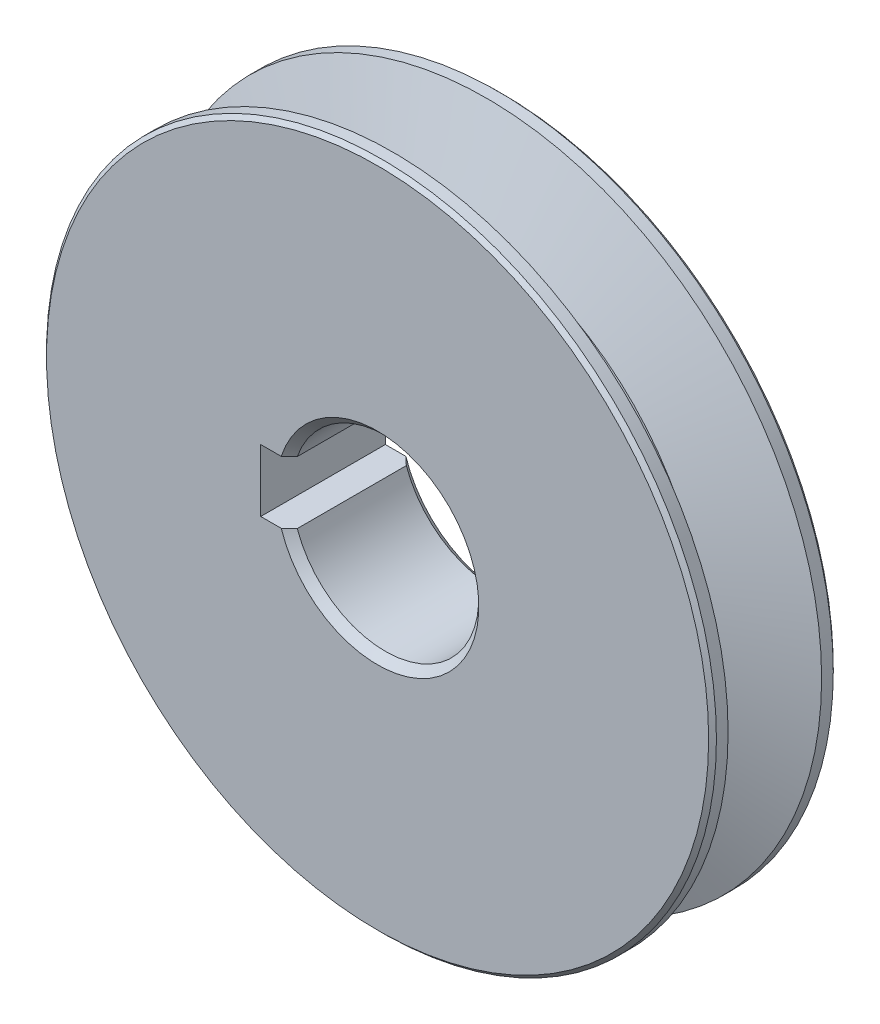
SolidWorks part; units mm, degrees
ref_plane "Front Plane" through (0, 0, 0) normal (0, 0, 1) x (1, 0, 0)
ref_plane "Top Plane" through (0, 0, 0) normal (0, 1, 0) x (1, 0, 0)
ref_plane "Right Plane" through (0, 0, 0) normal (1, 0, 0) x (0, 0, -1)
sketch "Sketch1" plane through (0, 0, 0) normal (0, 1, 0) x (1, 0, 0)
  line L0 (43, 8) -> (0, 8)
  line L1 (0, 8) -> (0, -8)
  line L2 (0, -8) -> (43, -8)
  line L3 (43, -8) -> (43, -6.0037)
  line L4 (43, -6.0037) -> (32, -2)
  line L5 (32, -2) -> (32, 2)
  line L6 (32, 2) -> (43, 6.0037)
  line L7 (43, 6.0037) -> (43, 8)
  line L8 (0, 8) -> (0, -8) construction
revolve "Revolve1" add sketch "Sketch1" angle 360 about L8
sketch "Sketch2" plane through (0, 0, 8) normal (0, 0, 1) x (1, 0, 0)
  line L0 (-15, -4) -> (-11.3137, -4)
  line L1 (-11.3137, 4) -> (-15, 4)
  line L2 (-15, 4) -> (-15, -4)
  arc A0 (-11.3137, -4) -> (-11.3137, 4) centre (0, 0) cw
extrude "Cut-Extrude1" cut sketch "Sketch2" against normal through all
sketch "Sketch3" plane through (0, 0, 0) normal (0, 1, 0) x (1, 0, 0)
  line L0 (12, 8) -> (0, 8)
  line L1 (0, 8) -> (0, -8)
  line L2 (0, -8) -> (12, -8)
  line L3 (12, -8) -> (12, 8)
  line L4 (0, 8) -> (0, -8) construction
revolve "Cut-Revolve1" cut sketch "Sketch3" angle 360 about L4
chamfer "Chamfer1" distance 1 angle 45 2 edges at (12, 0, 8) (12, 0, -8)
chamfer "Chamfer2" distance 0.5 angle 45 2 edges at (43, 0, 8) (43, 0, -8)
scale "Scale1" scale about centroid uniform scaling yes scale factor 0.75
